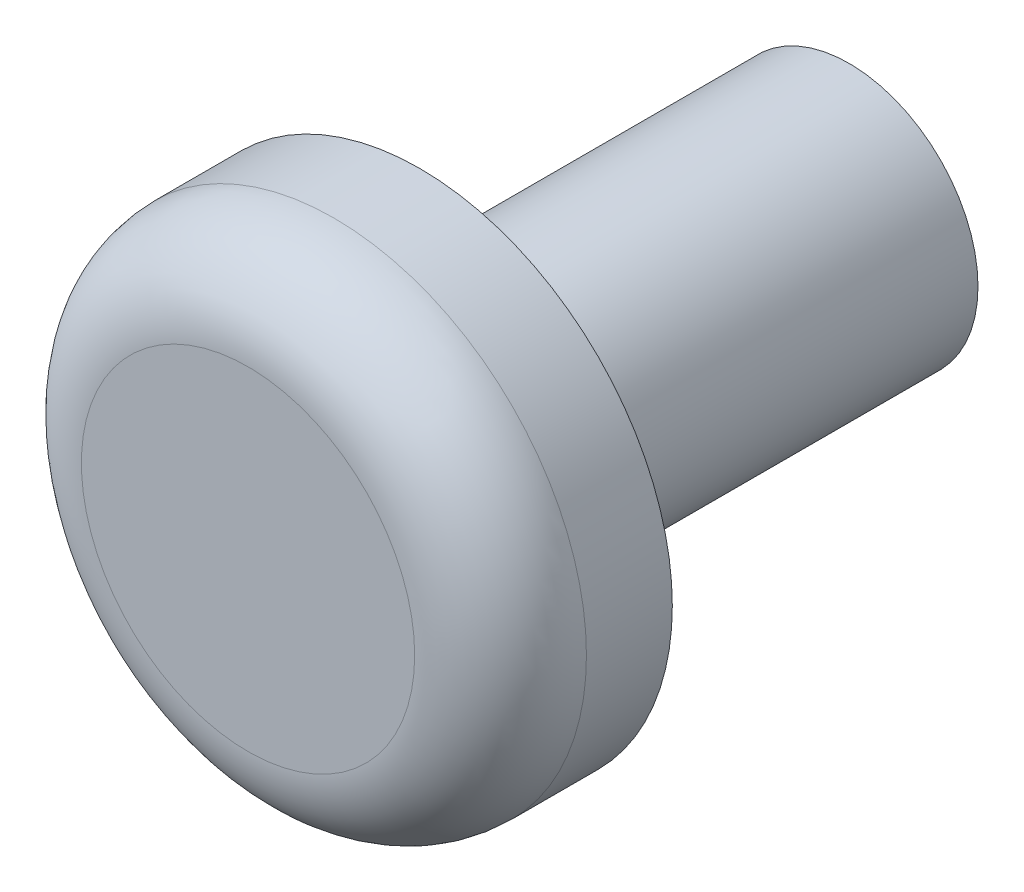
SolidWorks part; units mm, degrees
material "Plain Carbon Steel"
ref_plane "Спереди" through (0, 0, 0) normal (0, 0, 1) x (1, 0, 0)
ref_plane "Сверху" through (0, 0, 0) normal (0, 1, 0) x (1, 0, 0)
ref_plane "Справа" through (0, 0, 0) normal (1, 0, 0) x (0, 0, -1)
other "Configuration Table"
sketch "Sketch1" plane through (0, 0, 0) normal (0, 0, 1) x (1, 0, 0)
  circle A0 centre (0, 0) radius 1.5
  dimension "D1" = 3
extrude "Boss-Extrude1" add sketch "Sketch1" along normal blind 5
sketch "Sketch2" plane through (0, 0, 5) normal (0, 0, 1) x (1, 0, 0)
  circle A0 centre (0, 0) radius 2.9406
extrude "Boss-Extrude2" add sketch "Sketch2" along normal blind 2
fillet "Fillet1" radius 1 1 edges at (2.9406, 0, 7)
